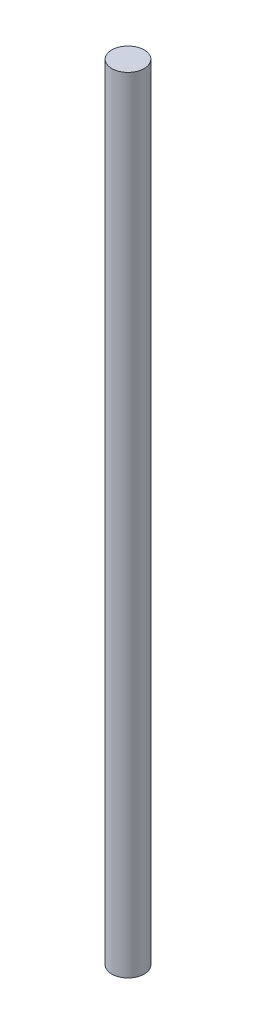
SolidWorks part; units mm, degrees
ref_plane "Front Plane" through (0, 0, 0) normal (0, 0, 1) x (1, 0, 0)
ref_plane "Top Plane" through (0, 0, 0) normal (0, 1, 0) x (1, 0, 0)
ref_plane "Right Plane" through (0, 0, 0) normal (1, 0, 0) x (0, 0, -1)
sketch "Sketch1" plane through (0, 0, 0) normal (0, 1, 0) x (1, 0, 0)
  circle A0 centre (0, 0) radius 2
extrude "Boss-Extrude1" add sketch "Sketch1" along normal blind 97
